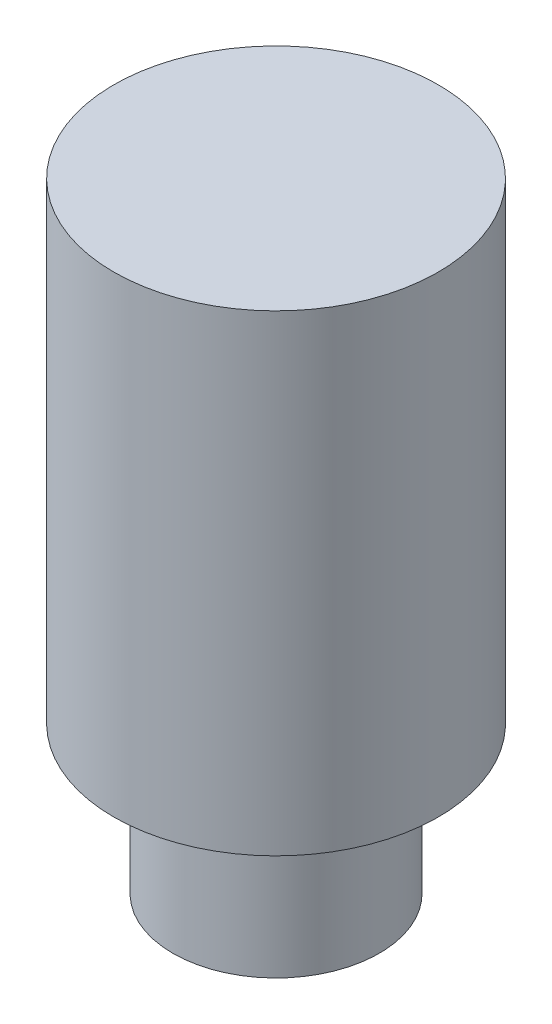
SolidWorks part; units mm, degrees
ref_plane "Front Plane" through (0, 0, 0) normal (0, 0, 1) x (1, 0, 0)
ref_plane "Top Plane" through (0, 0, 0) normal (0, 1, 0) x (1, 0, 0)
ref_plane "Right Plane" through (0, 0, 0) normal (1, 0, 0) x (0, 0, -1)
sketch "Sketch1" plane through (0, 0, 0) normal (0, 1, 0) x (1, 0, 0)
  circle A0 centre (0, 0) radius 3.5
  dimension "D1" = 7
extrude "Boss-Extrude1" add sketch "Sketch1" along normal blind 5
sketch "Sketch2" plane through (0, 5, 0) normal (0, 1, 0) x (1, 0, 0)
  circle A0 centre (0, 0) radius 5.5
  dimension "D1" = 11
extrude "Boss-Extrude2" add sketch "Sketch2" along normal blind 16
scale "Scale1" scale about centroid uniform scaling yes scale factor 0.225
